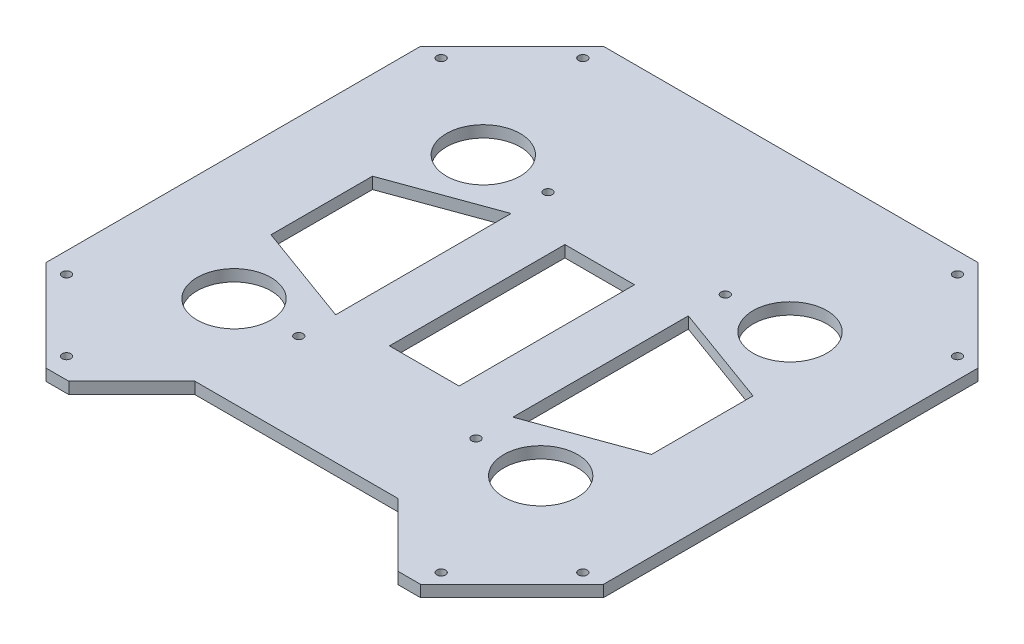
SolidWorks part; units mm, degrees
ref_plane "Front Plane" through (0, 0, 0) normal (0, 0, 1) x (1, 0, 0)
ref_plane "Top Plane" through (0, 0, 0) normal (0, 1, 0) x (1, 0, 0)
ref_plane "Right Plane" through (0, 0, 0) normal (1, 0, 0) x (0, 0, -1)
sketch "Sketch1" plane through (0, 0, 0) normal (0, 1, 0) x (1, 0, 0)
  line L0 (0, 0) -> (0, 724.3659) construction
  line L1 (0, 0) -> (205, 0)
  line L2 (305, 100) -> (305, 510)
  line L3 (205, 610) -> (-205, 610)
  line L4 (-305, 510) -> (-305, 100)
  line L6 (-305, 510) -> (-205, 610)
  line L7 (-205, 0) -> (205, 0)
  line L10 (0, 0) -> (205, 0)
  line L11 (305, 510) -> (205, 610)
  line L12 (305, 305) -> (-370.4931, 305) construction
  line L14 (-305, 100) -> (-205, 0)
  line L15 (305, 100) -> (205, 0)
  line L16 (-205, 610) -> (-305, 510)
  line L17 (-205, 610) -> (-136.4106, 541.4106)
  line L18 (-305, 510) -> (-236.4106, 441.4106)
  line L19 (-136.4106, 541.4106) -> (-236.4106, 441.4106)
  line L20 (305, 510) -> (205, 610)
  line L21 (305, 510) -> (236.4106, 441.4106)
  line L22 (136.4106, 541.4106) -> (236.4106, 441.4106)
  line L23 (205, 610) -> (136.4106, 541.4106)
  line L24 (305, 100) -> (236.4106, 168.5894)
  line L25 (305, 100) -> (205, 0)
  line L26 (136.4106, 68.5894) -> (236.4106, 168.5894)
  line L27 (205, 0) -> (136.4106, 68.5894)
  line L28 (-305, 100) -> (-205, 0)
  line L29 (-305, 100) -> (-236.4106, 168.5894)
  line L30 (-205, 0) -> (-136.4106, 68.5894)
  line L31 (-136.4106, 68.5894) -> (-236.4106, 168.5894)
  line L32 (205, 610) -> (136.4106, 541.4106)
  line L33 (205, 610) -> (305, 510)
  line L34 (136.4106, 541.4106) -> (236.4106, 441.4106)
  line L35 (305, 510) -> (236.4106, 441.4106)
  line L36 (-305, 100) -> (-205, 0)
  line L37 (-305, 100) -> (-236.4106, 168.5894)
  line L38 (-205, 0) -> (-136.4106, 68.5894)
  line L39 (-236.4106, 168.5894) -> (-136.4106, 68.5894)
  line L40 (236.4106, 168.5894) -> (136.4106, 68.5894)
  line L41 (236.4106, 168.5894) -> (305, 100)
  line L42 (136.4106, 68.5894) -> (205, 0)
  line L43 (305, 100) -> (205, 0)
  line L45 (0, 610) -> (-84.25, 610)
  line L46 (0, 0) -> (-84.25, 0)
  line L47 (-84.25, 610) -> (-84.25, 0)
  line L48 (84.25, 610) -> (84.25, 0)
  line L49 (-84.25, 610) -> (84.25, 610)
  line L50 (-84.25, 610) -> (-84.25, 0)
  line L51 (84.25, 610) -> (84.25, 0)
  line L52 (-84.25, 0) -> (84.25, 0)
  line L53 (-167.8213, 441.4106) -> (-97, 441.4106)
  line L54 (-84.25, 76.4) -> (84.25, 76.4)
  line L55 (-84.25, 76.4) -> (-84.25, 533.6)
  line L56 (84.25, 76.4) -> (84.25, 533.6)
  line L57 (-84.25, 533.6) -> (84.25, 533.6)
  line L70 (-305, 510) -> (-236.4106, 441.4106)
  circle A0 centre (-167.8213, 441.4106) radius 40.4
  circle A1 centre (-167.8213, 168.5894) radius 40.4
  circle A2 centre (167.8213, 168.5894) radius 40.4
  circle A3 centre (167.8213, 441.4106) radius 40.4
  arc A4 (-84.25, 76.4) -> (84.25, 76.4) centre (0, 76.4) ccw
  circle A9 centre (-97, 441.4106) radius 4.7625
  circle A10 centre (97, 441.4106) radius 4.7625
  circle A11 centre (97, 168.5894) radius 4.7625
  circle A12 centre (-97, 168.5894) radius 4.7625
  point P47 (-270.7053, 475.7053)
  dimension "D6" = 80.8
  dimension "D10" = 48.5
  dimension "D15" = 9.525
  dimension "D16" = 48.5
  dimension "D1" = 610
  dimension "D2" = 610
  dimension "D3" = 97
  dimension "D4" = 45
  dimension "D5" = 100
  dimension "D7" = 168.5
  dimension "D8" = 84.25
  dimension "D9" = 84.25
  dimension "D11" = 457.2
  dimension "D13" = 533.6
  dimension "D14" = 194
extrude "Boss-Extrude1" add sketch "Sketch1" along normal blind 12.7 contours L19 L17 L6 L18 | L39 A1 L31 L30 L7 L47 L3 L17 L19 A0 L18 L4 L29 | L30 L31 L39 L29 L14 | L48 L3 L47 L7 L1 | L34 A3 L22 L23 L3 L48 L10 L27 L26 A2 L40 L24 L2 L21 | L11 L23 L22 L34 L21 | L27 L15 L24 L40 L26 | L54 L55 L57 L56 | L49 L50 L52 L51
sketch "Sketch2" plane through (0, 12.7, 0) normal (0, 1, 0) x (1, 0, 0)
  line L4 (-205, 0) -> (-180, 0)
  line L5 (-180, 0) -> (-111, 69)
  line L6 (-180, 0) -> (180, 0)
  line L7 (180, 0) -> (111, 69)
  line L8 (111, 69) -> (-111, 69)
  line L10 (180, 0) -> (205, 0)
  line M5 (-205, 0) -> (205, 0)
  dimension "D1" = 25
  dimension "D2" = 25
  dimension "D3" = 45
  dimension "D4" = 69
  dimension "D5" = 45
extrude "Cut-Extrude1" cut sketch "Sketch2" against normal blind 5000 contours L7 L8 L5 M5
sketch "Sketch3" plane through (0, 12.7, 0) normal (0, 1, 0) x (1, 0, 0)
  line L0 (0, 0) -> (0, 610) construction
  line L1 (-305, 305) -> (305, 305) construction
  line L2 (-305, 100) -> (-205, 0) construction
  line L4 (-282.5423, 100) -> (-293.7711, 88.7711)
  line L5 (205, 610) -> (-205, 610) construction
  line L6 (-305, 510) -> (-305, 100) construction
  line L7 (305, 100) -> (305, 510) construction
  line L8 (-180, 0) -> (-111, 69) construction
  circle A0 centre (-205, 22.4577) radius 4.7625
  circle A1 centre (205, 22.4577) radius 4.7625
  circle A2 centre (-282.5423, 100) radius 4.7625
  circle A3 centre (282.5423, 100) radius 4.7625
  circle A4 centre (282.5423, 510) radius 4.7625
  circle A5 centre (205, 587.5423) radius 4.7625
  circle A6 centre (-205, 587.5423) radius 4.7625
  circle A7 centre (-282.5423, 510) radius 4.7625
  dimension "D1" = 9.525
  dimension "D2" = 9.525
  dimension "D6" = 15.88
  dimension "D5" = 33.5577
  dimension "D3" = 15.88
  dimension "D4" = 15.88
  dimension "D7" = 15.88
extrude "Cut-Extrude2" cut sketch "Sketch3" against normal blind 5000 contours A2 | A0 | A1 | A3 | A4 | A5 | A6 | A7
sketch "Sketch4" plane through (0, 12.7, 0) normal (0, 1, 0) x (1, 0, 0)
  line L0 (0, 610) -> (0, 69)
  line L1 (0, 610) -> (69.7563, 610)
  line L2 (0, 69) -> (69.7563, 69)
  line L3 (69.7563, 610) -> (69.7563, 69)
  line L4 (205, 610) -> (-205, 610) construction
  line L5 (111, 69) -> (-111, 69) construction
  line L6 (0, 69) -> (0, 610)
  line L7 (0, 69) -> (-74.0097, 69)
  line L8 (0, 610) -> (-74.0097, 610)
  line L9 (-74.0097, 69) -> (-74.0097, 610)
  line L10 (0, 0) -> (0, 637.1931) construction
  line L19 (-97, 401.0106) -> (-97, 208.9894)
  line L20 (-97, 208.9894) -> (-208.2213, 249.4706)
  line L21 (-208.2213, 249.4706) -> (-208.2213, 360.5294)
  line L22 (-97, 441.4106) -> (-97, 168.5894)
  line L23 (-208.2213, 441.4106) -> (-208.2213, 168.5894)
  line L24 (-208.2213, 360.5294) -> (-97, 401.0106)
  line L25 (-208.2213, 441.4106) -> (-167.8213, 441.4106)
  line L26 (-167.8213, 401.0106) -> (-97, 401.0106)
  line L27 (-167.8213, 208.9894) -> (-97, 208.9894)
  line L28 (208.2213, 249.4706) -> (208.2213, 360.5294)
  line L29 (97, 208.9894) -> (208.2213, 249.4706)
  line L30 (97, 401.0106) -> (97, 208.9894)
  line L31 (208.2213, 360.5294) -> (97, 401.0106)
  circle A0 centre (-167.8213, 441.4106) radius 40.4 construction
  circle A1 centre (-167.8213, 168.5894) radius 40.4 construction
  dimension "D1" = 70.8213
  dimension "D2" = 70.8213
  dimension "D3" = 20
  dimension "D4" = 20
extrude "Cut-Extrude3" cut sketch "Sketch4" against normal blind 20 contours L24 L21 L20 L19 | L28 L31 L30 L29
sketch "Sketch5" plane through (0, 12.7, 0) normal (0, 1, 0) x (1, 0, 0)
  line L5 (-97, 401.0106) -> (97, 401.0106)
  line L6 (-97, 401.0106) -> (-97, 208.9894)
  line L7 (97, 401.0106) -> (97, 208.9894)
  line L8 (-97, 208.9894) -> (97, 208.9894)
  line L13 (0, 0) -> (0, 637.5657) construction
  line L14 (38.1, 401.0106) -> (38.1, 208.9894)
  line L15 (-38.1, 401.0106) -> (38.1, 401.0106)
  line L16 (-38.1, 401.0106) -> (-38.1, 208.9894)
  line L17 (-38.1, 208.9894) -> (38.1, 208.9894)
  line L18 (0, 401.0106) -> (0, 208.9894)
  dimension "D1" = 38.1
extrude "Cut-Extrude4" cut sketch "Sketch5" against normal blind 78.232 contours L18 L5 L16 L8 | L15 L18 L17 L14
